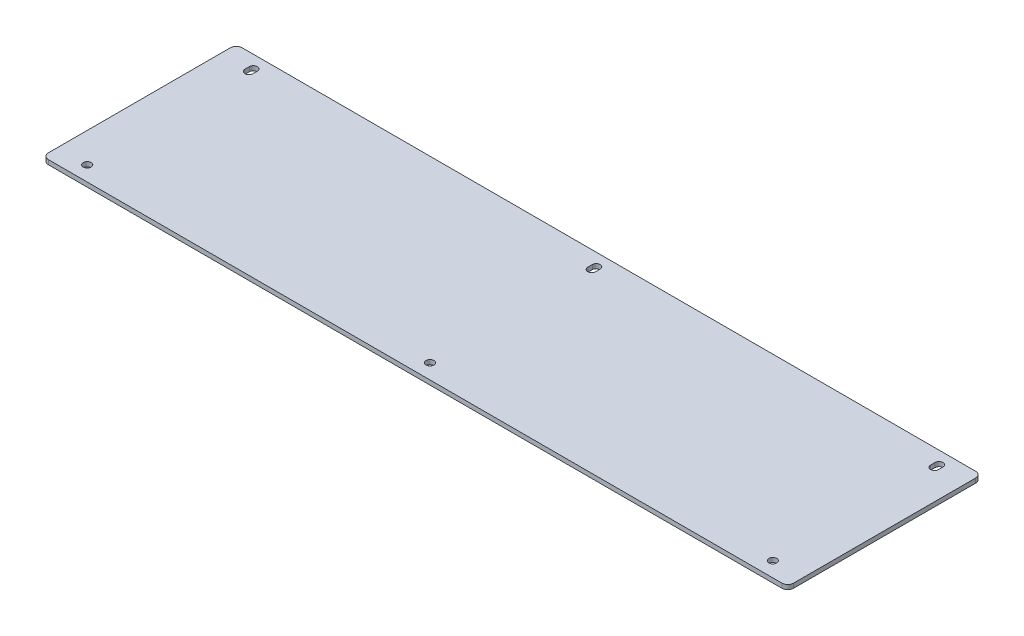
SolidWorks part; units mm, degrees
ref_plane "Front Plane" through (0, 0, 0) normal (0, 0, 1) x (1, 0, 0)
ref_plane "Top Plane" through (0, 0, 0) normal (0, 1, 0) x (1, 0, 0)
ref_plane "Right Plane" through (0, 0, 0) normal (1, 0, 0) x (0, 0, -1)
sketch "Sketch1" plane through (0, 0, 0) normal (0, 1, 0) x (1, 0, 0)
  line L1 (-250, -65) -> (250, -65)
  line L2 (-250, -65) -> (-250, 65)
  line L3 (-250, 65) -> (250, 65)
  line L4 (250, -65) -> (250, 65)
  line L5 (-250, -65) -> (250, 65) construction
  line L6 (-250, 65) -> (250, -65) construction
  point P0 (0, 0)
  dimension "D1" = 500
  dimension "D2" = 130
extrude "Boss-Extrude1" add sketch "Sketch1" along normal blind 3
fillet "Fillet1" radius 4 4 edges at (-250, 1.5, 65) (-250, 1.5, -65) (250, 1.5, -65) (250, 1.5, 65)
hole_wizard "Ø5.3 (5.3) Diameter Hole1" positions "Sketch4" profile "Sketch5" hole size "Ø5.3" standard "ANSI Metric" end condition through all
sketch "Sketch4" plane through (0, 3, 0) normal (0, 1, 0) x (1, 0, 0)
  line L1 (-230, -55) -> (230, -55)
  line L2 (-230, -55) -> (-230, 55)
  line L3 (-230, 55) -> (230, 55)
  line L4 (230, -55) -> (230, 55)
  line L5 (-230, -55) -> (230, 55) construction
  line L6 (-230, 55) -> (230, -55) construction
  line L7 (246, 65) -> (-246, 65) construction
  line L8 (250, -61) -> (250, 61) construction
  point P2 (230, 55)
  point P59 (-230, -55)
  point P60 (-230, 55)
  point P61 (230, -55)
  point P68 (0, 55)
  point P70 (0, -55)
  dimension "D1" = 10
  dimension "D2" = 20
sketch "Sketch5" plane through (230, 3, -55) normal (1, 0, 0) x (0, 0, 1)
  line L0 (0, 0) -> (0, 3)
  line L1 (0, 3) -> (2.65, 3)
  line L2 (2.65, 3) -> (2.65, 0)
  line L5 (2.65, 0) -> (0, 0)
  line L11 (0, -6.35) -> (0, 107.95) construction
  dimension "Thru Hole Dia." = 5.3
  dimension "Thru Hole Depth" = 3
sketch "Sketch6" plane through (0, 3, 0) normal (0, 1, 0) x (1, 0, 0)
  line L0 (-230, 53.5) -> (-230, 56.5) construction
  line L1 (-232.65, 53.5) -> (-232.65, 56.5)
  line L2 (-227.35, 53.5) -> (-227.35, 56.5)
  line L3 (0, 53.5) -> (0, 56.5) construction
  line L4 (-2.65, 53.5) -> (-2.65, 56.5)
  line L5 (2.65, 53.5) -> (2.65, 56.5)
  line L6 (230, 53.5) -> (230, 56.5) construction
  line L7 (227.35, 53.5) -> (227.35, 56.5)
  line L8 (232.65, 53.5) -> (232.65, 56.5)
  arc A0 (-232.65, 53.5) -> (-227.35, 53.5) centre (-230, 53.5) ccw
  arc A1 (-227.35, 56.5) -> (-232.65, 56.5) centre (-230, 56.5) ccw
  circle A2 centre (-230, 55) radius 2.65 construction
  arc A3 (-2.65, 53.5) -> (2.65, 53.5) centre (0, 53.5) ccw
  arc A4 (2.65, 56.5) -> (-2.65, 56.5) centre (0, 56.5) ccw
  circle A5 centre (0, 55) radius 2.65 construction
  arc A6 (227.35, 53.5) -> (232.65, 53.5) centre (230, 53.5) ccw
  arc A7 (232.65, 56.5) -> (227.35, 56.5) centre (230, 56.5) ccw
  circle A8 centre (230, 55) radius 2.65 construction
  point P2 (-230, 55)
  point P12 (0, 55)
  point P23 (230, 55)
  dimension "D1" = 3
extrude "Cut-Extrude1" cut sketch "Sketch6" against normal through all
